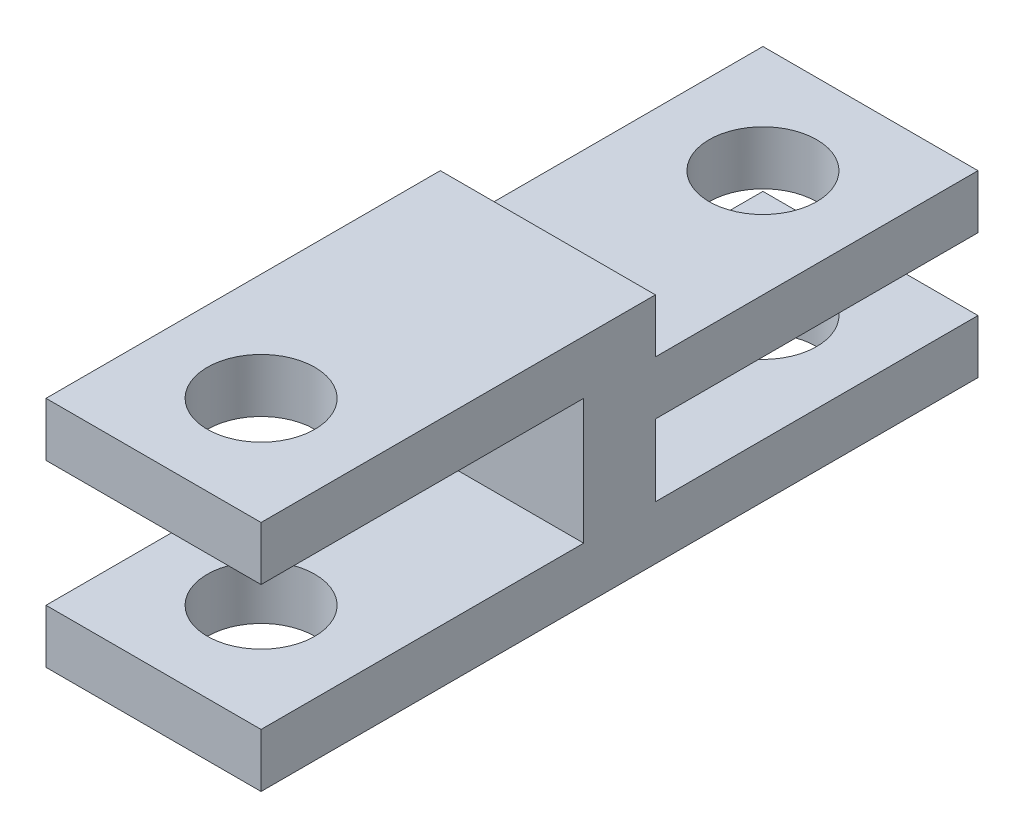
SolidWorks part; units mm, degrees
ref_plane "Front Plane" through (0, 0, 0) normal (0, 0, 1) x (1, 0, 0)
ref_plane "Top Plane" through (0, 0, 0) normal (0, 1, 0) x (1, 0, 0)
ref_plane "Right Plane" through (0, 0, 0) normal (1, 0, 0) x (0, 0, -1)
sketch "Sketch1" plane through (0, 0, 0) normal (1, 0, 0) x (0, 0, -1)
  line L12 (0, 0) -> (-20, 0)
  line L13 (-20, 0) -> (-20, 1.5)
  line L14 (-20, 1.5) -> (-11, 1.5)
  line L15 (-11, 1.5) -> (-11, 5)
  line L16 (-11, 5) -> (-20, 5)
  line L17 (-20, 5) -> (-20, 6.5)
  line L18 (-20, 6.5) -> (-9, 6.5)
  line L19 (-9, 6.5) -> (-9, 5)
  line L20 (-9, 5) -> (0, 5)
  line L21 (0, 5) -> (0, 3.5)
  line L22 (0, 3.5) -> (-9, 3.5)
  line L23 (-9, 3.5) -> (-9, 1.5)
  line L24 (-9, 1.5) -> (0, 1.5)
  line L25 (0, 1.5) -> (0, 0)
  dimension "D5" = 20
  dimension "D6" = 9
  dimension "D7" = 3.5
  dimension "D8" = 1.5
  dimension "D9" = 1.5
  dimension "D10" = 2
  dimension "D11" = 1.5
  dimension "D12" = 1.5
extrude "Boss-Extrude1" add sketch "Sketch1" along normal blind 6
sketch "Sketch2" plane through (0, 0, 0) normal (0, -1, 0) x (1, 0, 0)
  line L0 (0, 3) -> (6, 3) construction
  line L1 (0, 20) -> (0, 0) construction
  line L2 (6, 20) -> (6, 0) construction
  line L3 (0, 17) -> (6, 17) construction
  line L4 (6, 0) -> (0, 0) construction
  line L5 (6, 20) -> (0, 20) construction
  circle A0 centre (3, 3) radius 1.5
  circle A1 centre (3, 17) radius 1.5
  point P13 (3, 3)
  point P15 (3, 17)
  dimension "D1" = 3
  dimension "D2" = 3
  dimension "D3" = 3
  dimension "D4" = 3
extrude "Cut-Extrude1" cut sketch "Sketch2" against normal through all both and the other way through all
